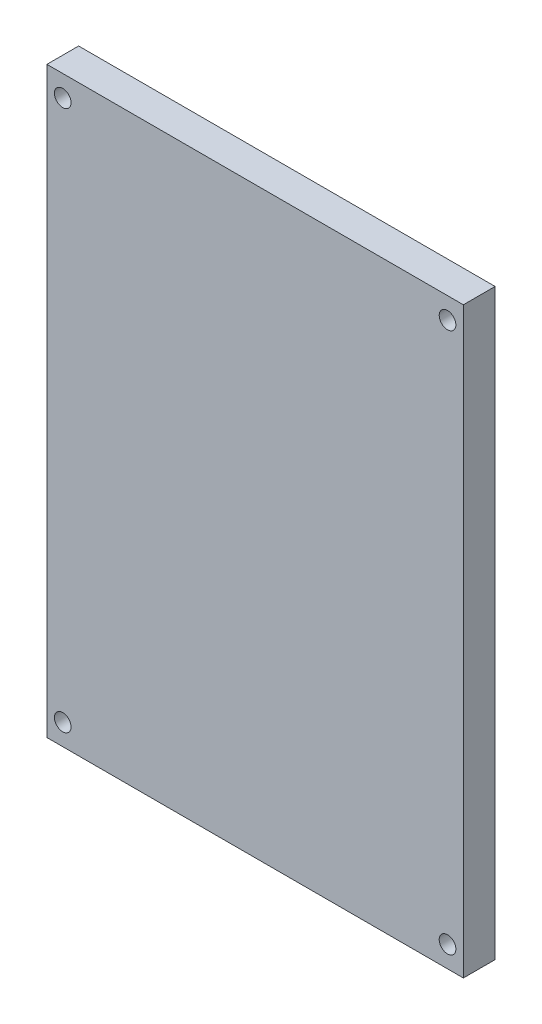
SolidWorks part; units mm, degrees
material "Default"
ref_plane "Top" through (0, 0, 0) normal (0, 0, 1) x (1, 0, 0)
ref_plane "Right" through (0, 0, 0) normal (0, 1, 0) x (1, 0, 0)
ref_plane "Front" through (0, 0, 0) normal (1, 0, 0) x (0, 0, -1)
sketch "Sketch1" plane through (0, 0, 0) normal (0, 0, 1) x (1, 0, 0)
  line L1 (-46.8217, 28.9193) -> (3.1783, 28.9193)
  line L2 (-46.8217, 28.9193) -> (-46.8217, -41.0807)
  line L3 (-46.8217, -41.0807) -> (3.1783, -41.0807)
  line L4 (3.1783, 28.9193) -> (3.1783, -41.0807)
  dimension "D1" = 50
  dimension "D2" = 70
extrude "Boss-Extrude1" add sketch "Sketch1" along normal blind 3.81
sketch "Sketch2" plane through (0, 0, 3.81) normal (0, 0, 1) x (1, 0, 0)
  line L0 (-21.8217, 28.9193) -> (-21.8217, -41.0807) construction
  line L1 (3.1783, 28.9193) -> (-46.8217, 28.9193) construction
  line L2 (-46.8217, -41.0807) -> (3.1783, -41.0807) construction
  line L3 (-21.8217, -6.0807) -> (-82.8713, -6.0807) construction
  circle A0 centre (-44.9217, 26.3692) radius 1
  circle A1 centre (1.2783, 26.3692) radius 1
  circle A2 centre (1.2783, -38.5306) radius 1
  circle A3 centre (-44.9217, -38.5306) radius 1
  dimension "D1" = 2
  dimension "D2" = 23.1
extrude "Cut-Extrude1" cut sketch "Sketch2" against normal up to surface (3.81 mm away) up to face at (-21.8217, -6.0807, 0)
